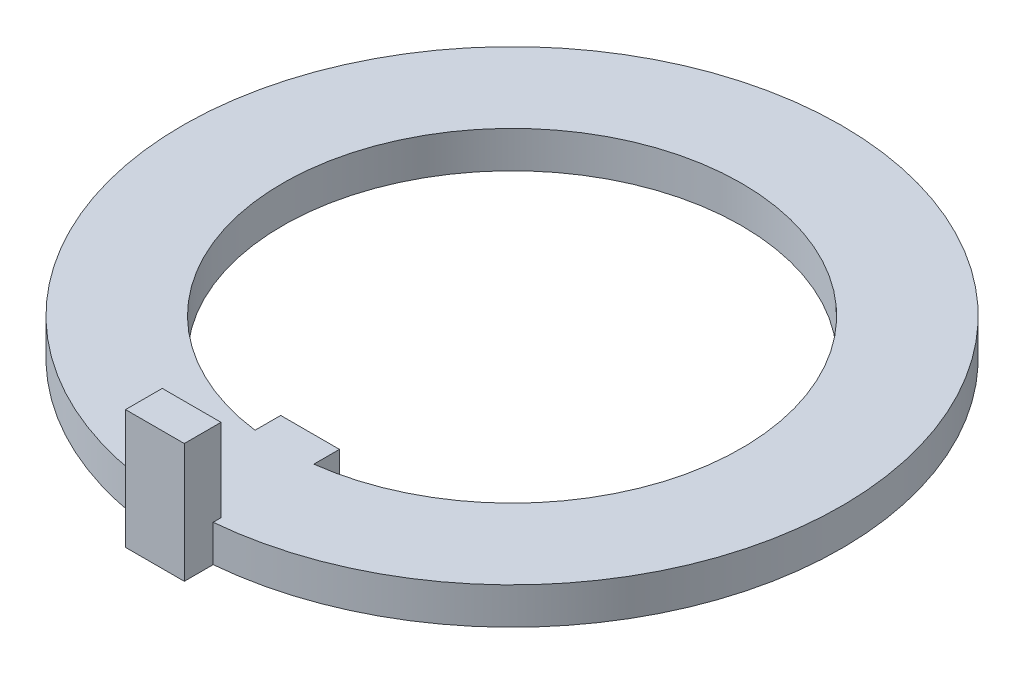
SolidWorks part; units mm, degrees
material "Plain Carbon Steel"
ref_plane "Front Plane" through (0, 0, 0) normal (0, 0, 1) x (1, 0, 0)
ref_plane "Top Plane" through (0, 0, 0) normal (0, 1, 0) x (1, 0, 0)
ref_plane "Right Plane" through (0, 0, 0) normal (1, 0, 0) x (0, 0, -1)
sketch "Sketch1" plane through (0, 0, 0) normal (0, 1, 0) x (1, 0, 0)
  line L0 (0, -6.35) -> (0, -9.1186) construction
  line L1 (0.8128, -6.2978) -> (0.8128, -5.588)
  line L2 (0.8128, -9.8806) -> (-0.8128, -9.8806)
  line L3 (0.8128, -9.8806) -> (0.8128, -9.0823)
  line L4 (0.8128, -5.588) -> (-0.8128, -5.588)
  line L5 (-0.8128, -9.8806) -> (-0.8128, -9.0823)
  line L6 (0.8128, -9.8806) -> (-0.8128, -5.588) construction
  line L7 (0.8128, -5.588) -> (-0.8128, -9.8806) construction
  line L8 (-0.8128, -6.2978) -> (-0.8128, -5.588)
  arc A0 (0.8128, -9.0823) -> (-0.8128, -9.0823) centre (0, 0) ccw
  arc A1 (0.8128, -6.2978) -> (-0.8128, -6.2978) centre (0, 0) ccw
  point P6 (0, -7.7343)
  dimension "D1" = 18.2372
  dimension "D2" = 12.7
  dimension "D3" = 1.6256
  dimension "D4" = 0.762
extrude "Boss-Extrude1" add sketch "Sketch1" along normal blind 1.016
sketch "Sketch2" plane through (0, 1.016, 0) normal (0, 1, 0) x (1, 0, 0)
  line L0 (0.8128, -9.8806) -> (0.8128, -9.0823) construction
  line L1 (-0.8128, -9.8806) -> (0.8128, -9.8806)
  line L2 (-0.8128, -9.8806) -> (-0.8128, -8.8646)
  line L3 (-0.8128, -8.8646) -> (0.8128, -8.8646)
  line L4 (0.8128, -9.8806) -> (0.8128, -8.8646)
  dimension "D1" = 1.016
extrude "Boss-Extrude2" add sketch "Sketch2" along normal blind 2.286
